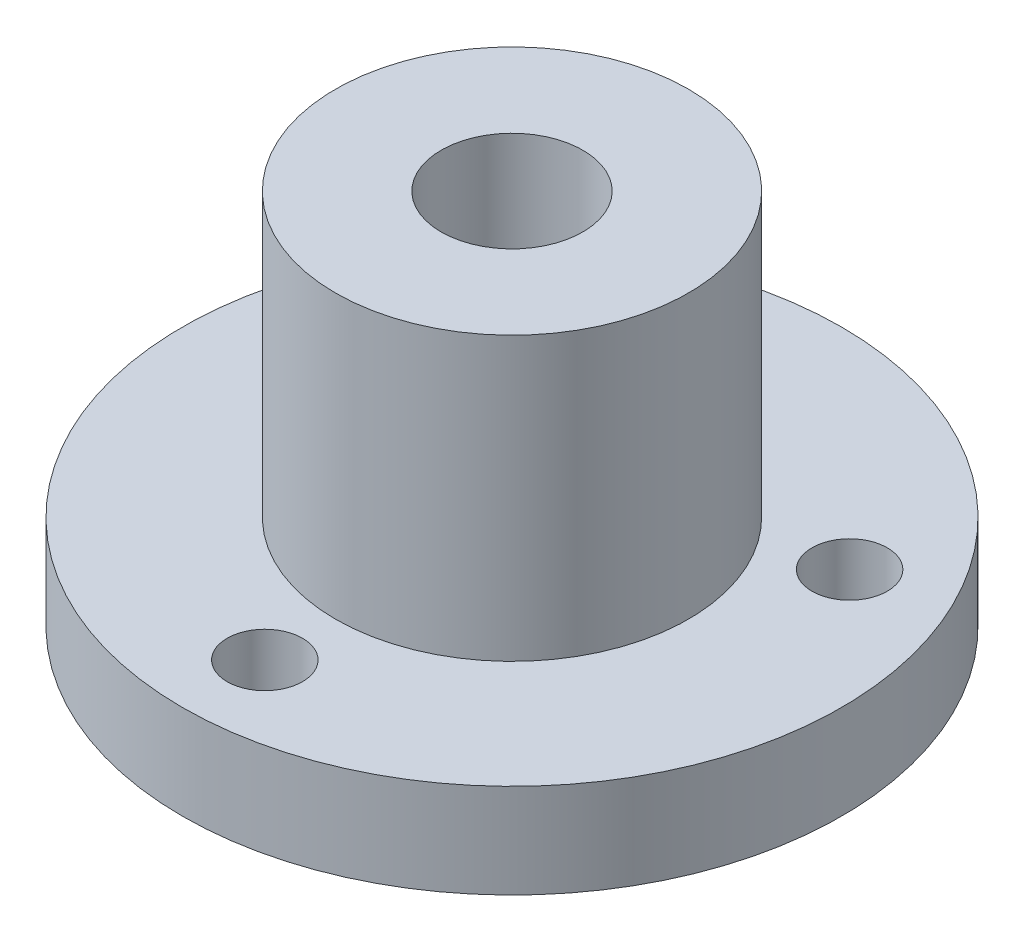
SolidWorks part; units mm, degrees
ref_plane "Front Plane" through (0, 0, 0) normal (0, 0, 1) x (1, 0, 0)
ref_plane "Top Plane" through (0, 0, 0) normal (0, 1, 0) x (1, 0, 0)
ref_plane "Right Plane" through (0, 0, 0) normal (1, 0, 0) x (0, 0, -1)
sketch "Sketch2" plane through (0, 0, 0) normal (0, 1, 0) x (1, 0, 0)
  circle A0 centre (0, 0) radius 14
extrude "Boss-Extrude1" add sketch "Sketch2" along normal blind 4
sketch "Sketch3" plane through (0, 4, 0) normal (0, 1, 0) x (1, 0, 0)
  circle A0 centre (0, 0) radius 7.5
extrude "Boss-Extrude2" add sketch "Sketch3" along normal blind 12
sketch "Sketch4" plane through (0, 16, 0) normal (0, 1, 0) x (1, 0, 0)
  circle A0 centre (0, 0) radius 3.01
extrude "Cut-Extrude1" cut sketch "Sketch4" against normal through all
sketch "Sketch5" plane through (0, 4, 0) normal (0, 1, 0) x (1, 0, 0)
  circle A0 centre (0, 0) radius 10.5
  circle A1 centre (0, -10.5) radius 1.6
  circle A2 centre (0, -10.5) radius 10.5
  circle A3 centre (0, -10.5) radius 10.5
  circle A4 centre (9.0933, -5.25) radius 10.5
  circle A5 centre (9.0933, 5.25) radius 10.5
  circle A6 centre (0, 10.5) radius 10.5
  circle A7 centre (-9.0933, 5.25) radius 10.5
  circle A8 centre (0, 0) radius 14
  circle A9 centre (-9.0933, -5.25) radius 10.5
  circle A10 centre (9.0933, 5.25) radius 1.6
  circle A11 centre (-9.0933, 5.25) radius 1.6
extrude "Cut-Extrude2" cut sketch "Sketch5" against normal blind 12 contours A1 | A10 | A11
